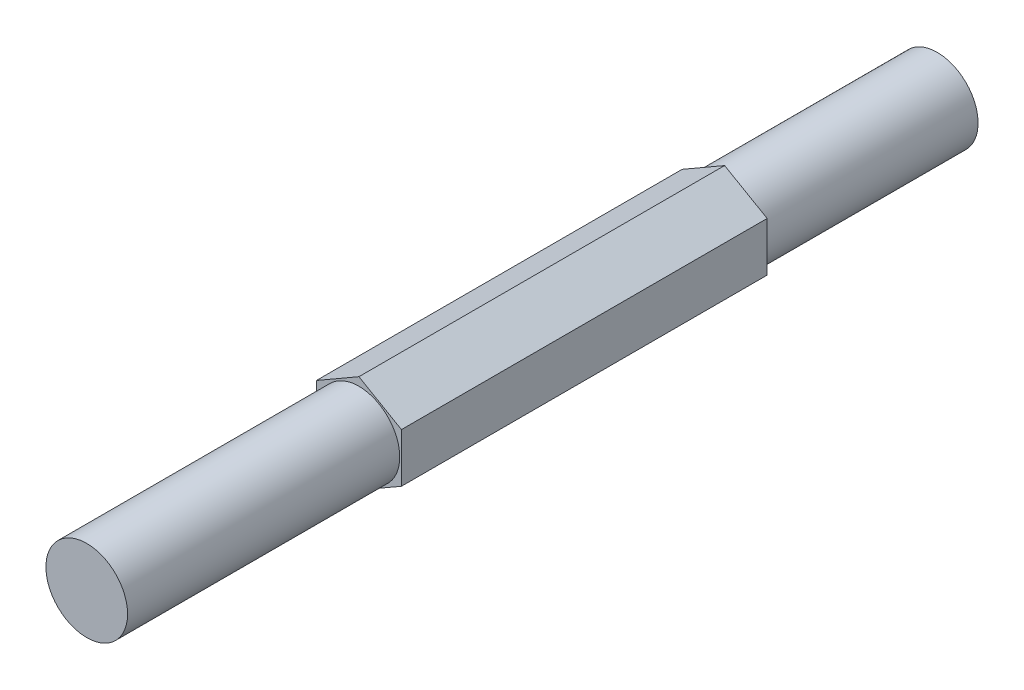
SolidWorks part; units mm, degrees
material "1060 Alloy"
ref_plane "Front Plane" through (0, 0, 0) normal (0, 0, 1) x (1, 0, 0)
ref_plane "Top Plane" through (0, 0, 0) normal (0, 1, 0) x (1, 0, 0)
ref_plane "Right Plane" through (0, 0, 0) normal (1, 0, 0) x (0, 0, -1)
sketch "Sketch2" plane through (0, 0, 0) normal (0, 0, 1) x (1, 0, 0)
  line L1 (0, 3.6662) -> (-3.175, 1.8331)
  line L2 (-3.175, 1.8331) -> (-3.175, -1.8331)
  line L3 (-3.175, -1.8331) -> (0, -3.6662)
  line L4 (0, -3.6662) -> (3.175, -1.8331)
  line L5 (3.175, -1.8331) -> (3.175, 1.8331)
  line L6 (3.175, 1.8331) -> (0, 3.6662)
  circle A0 centre (0, 0) radius 3.175 construction
  point P10 (0, 0)
  dimension "D1" = 6.35
extrude "Boss-Extrude1" add sketch "Sketch2" along normal blind 63.5
sketch "Sketch3" plane through (0, 0, 63.5) normal (0, 0, 1) x (1, 0, 0)
  circle A0 centre (0, 0) radius 3.048
  dimension "D1" = 6.096
extrude "Cut-Extrude1" cut sketch "Sketch3" against normal blind 20.32 flip side to cut
sketch "Sketch4" plane through (0, 0, 0) normal (0, 0, -1) x (-1, 0, 0)
  circle A0 centre (0, 0) radius 3.048
  dimension "D1" = 6.096
extrude "Cut-Extrude2" cut sketch "Sketch4" against normal blind 15.875 flip side to cut
